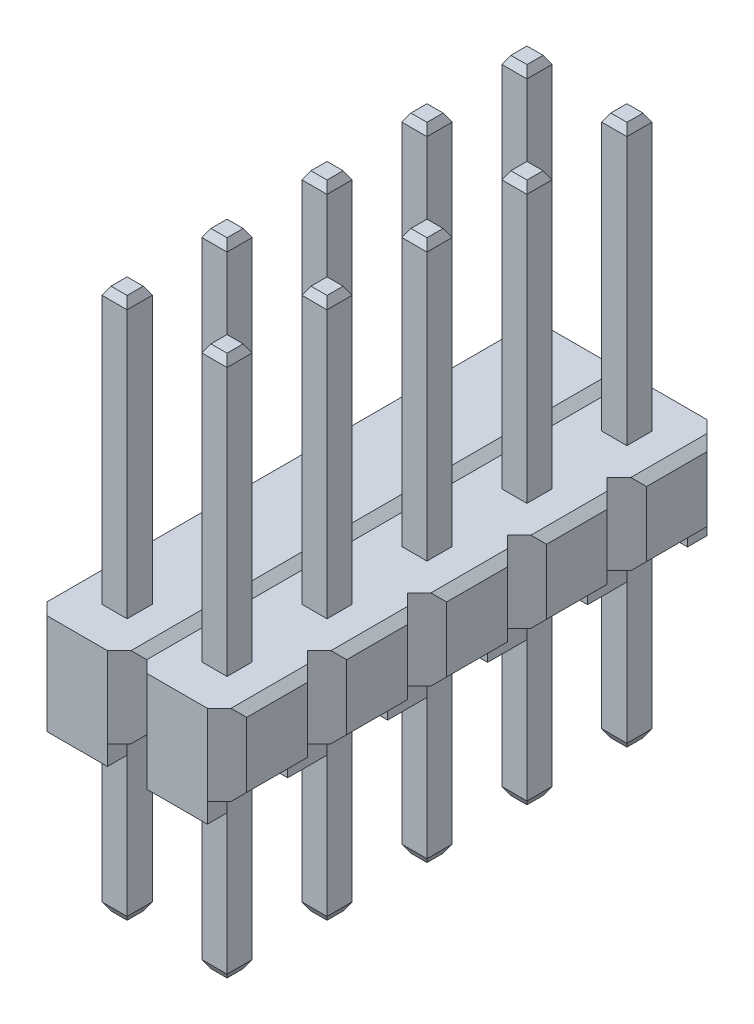
SolidWorks part; units mm, degrees
ref_plane "Front Plane" through (0, 0, 0) normal (0, 0, 1) x (1, 0, 0)
ref_plane "Top Plane" through (0, 0, 0) normal (0, 1, 0) x (1, 0, 0)
ref_plane "Right Plane" through (0, 0, 0) normal (1, 0, 0) x (0, 0, -1)
sketch "Sketch1" plane through (0, 0, 0) normal (0, 1, 0) x (1, 0, 0)
  line L0 (0, 0.77) -> (0.5, 1.27)
  line L1 (0, 4.31) -> (-0.5, 3.81)
  line L2 (2.04, 1.27) -> (2.54, 0.77)
  line L3 (2.54, 0.77) -> (2.54, -0.77)
  line L4 (2.54, -0.77) -> (2.04, -1.27)
  line L5 (-2.54, 0) -> (2.54, 0) construction
  line L6 (0.5, -1.27) -> (0, -0.77)
  line L7 (-2.54, 3.31) -> (-2.04, 3.81)
  line L8 (-55, 0) -> (55, 0) construction
  line L9 (-2.54, -0.77) -> (-2.54, 0.77)
  line L10 (-1.59, -0.32) -> (-0.95, -0.32)
  line L11 (0.95, -0.32) -> (1.59, -0.32)
  line L12 (0.95, -0.32) -> (0.95, 0.32)
  line L13 (0.95, 0.32) -> (1.59, 0.32)
  line L14 (1.59, -0.32) -> (1.59, 0.32)
  line L15 (-2.54, 0.77) -> (-2.04, 1.27)
  line L16 (-0.95, -0.32) -> (-0.95, 0.32)
  line L17 (-1.59, 0.32) -> (-0.95, 0.32)
  line L18 (0, -0.77) -> (-0.5, -1.27)
  line L19 (-2.04, -1.27) -> (-2.54, -0.77)
  line L20 (-0.5, 3.81) -> (0, 3.31)
  line L21 (-1.59, -0.32) -> (-1.59, 0.32)
  line L22 (1.59, 4.76) -> (1.59, 5.4)
  line L23 (-0.5, 1.27) -> (0, 0.77)
  line L24 (2.04, 3.81) -> (2.54, 3.31)
  line L25 (2.54, 1.77) -> (2.04, 1.27)
  line L26 (0, -55) -> (0, 55) construction
  line L27 (0.95, 2.86) -> (1.59, 2.86)
  line L28 (0.95, 2.22) -> (1.59, 2.22)
  line L29 (-2.54, 1.77) -> (-2.54, 3.31)
  line L30 (-1.59, 2.22) -> (-1.59, 2.86)
  line L31 (-0.95, 2.22) -> (-0.95, 2.86)
  line L32 (0, 1.77) -> (-0.5, 1.27)
  line L35 (2.54, 3.31) -> (2.54, 1.77)
  line L36 (0, 3.31) -> (0.5, 3.81)
  line L37 (0.5, 1.27) -> (0, 1.77)
  line L38 (-1.59, 2.22) -> (-0.95, 2.22)
  line L39 (0.95, 2.22) -> (0.95, 2.86)
  line L40 (1.59, 2.22) -> (1.59, 2.86)
  line L41 (-2.04, 1.27) -> (-2.54, 1.77)
  line L42 (-1.59, 2.86) -> (-0.95, 2.86)
  line L43 (0, -4.31) -> (0.5, -3.81)
  line L44 (-2.04, 6.35) -> (-0.5, 6.35)
  line L45 (-0.5, 6.35) -> (0, 5.85)
  line L46 (-1.59, 4.76) -> (-1.59, 5.4)
  line L47 (0.95, 4.76) -> (1.59, 4.76)
  line L48 (2.54, 5.85) -> (2.54, 4.31)
  line L49 (-2.04, 3.81) -> (-2.54, 4.31)
  line L50 (2.04, -3.81) -> (2.54, -4.31)
  line L51 (-1.59, 4.76) -> (-0.95, 4.76)
  line L52 (2.54, -4.31) -> (2.54, -5.85)
  line L53 (0, 5.85) -> (0.5, 6.35)
  line L54 (2.54, 4.31) -> (2.04, 3.81)
  line L55 (2.04, 6.35) -> (2.54, 5.85)
  line L56 (0.95, 5.4) -> (1.59, 5.4)
  line L57 (-2.54, 5.85) -> (-2.04, 6.35)
  line L58 (-2.54, 4.31) -> (-2.54, 5.85)
  line L59 (-1.59, 5.4) -> (-0.95, 5.4)
  line L60 (-0.95, 4.76) -> (-0.95, 5.4)
  line L61 (0.5, 3.81) -> (0, 4.31)
  line L62 (0.5, 6.35) -> (2.04, 6.35)
  line L63 (0.95, 4.76) -> (0.95, 5.4)
  line L64 (2.54, -5.85) -> (2.04, -6.35)
  line L65 (2.04, -6.35) -> (0.5, -6.35)
  line L66 (0.5, -6.35) -> (0, -5.85)
  line L67 (-2.54, -1.77) -> (-2.04, -1.27)
  line L68 (-0.5, -6.35) -> (-2.04, -6.35)
  line L69 (-2.54, -5.85) -> (-2.54, -4.31)
  line L70 (-1.59, -5.4) -> (-0.95, -5.4)
  line L71 (0.95, -5.4) -> (1.59, -5.4)
  line L72 (0.95, -5.4) -> (0.95, -4.76)
  line L73 (0.95, -4.76) -> (1.59, -4.76)
  line L74 (1.59, -5.4) -> (1.59, -4.76)
  line L75 (-2.54, -4.31) -> (-2.04, -3.81)
  line L76 (-0.95, -5.4) -> (-0.95, -4.76)
  line L77 (-1.59, -4.76) -> (-0.95, -4.76)
  line L78 (0, -5.85) -> (-0.5, -6.35)
  line L79 (-2.04, -6.35) -> (-2.54, -5.85)
  line L80 (-0.5, -1.27) -> (0, -1.77)
  line L81 (-1.59, -5.4) -> (-1.59, -4.76)
  line L82 (-0.5, -3.81) -> (0, -4.31)
  line L83 (2.04, -1.27) -> (2.54, -1.77)
  line L84 (2.54, -3.31) -> (2.04, -3.81)
  line L86 (0.95, -2.22) -> (1.59, -2.22)
  line L87 (0.95, -2.86) -> (1.59, -2.86)
  line L88 (-2.54, -3.31) -> (-2.54, -1.77)
  line L89 (-1.59, -2.86) -> (-1.59, -2.22)
  line L90 (-0.95, -2.86) -> (-0.95, -2.22)
  line L91 (0, -3.31) -> (-0.5, -3.81)
  line L92 (2.54, -1.77) -> (2.54, -3.31)
  line L93 (0, -1.77) -> (0.5, -1.27)
  line L94 (0.5, -3.81) -> (0, -3.31)
  line L95 (-1.59, -2.86) -> (-0.95, -2.86)
  line L96 (0.95, -2.86) -> (0.95, -2.22)
  line L97 (1.59, -2.86) -> (1.59, -2.22)
  line L98 (-2.04, -3.81) -> (-2.54, -3.31)
  line L99 (-1.59, -2.22) -> (-0.95, -2.22)
  dimension "D1" = 12.7
  dimension "D2" = 6.35
  dimension "D3" = 5.08
  dimension "D4" = 2.54
  dimension "D5" = 2.54
extrude "Boss-Extrude1" add sketch "Sketch1" against normal blind 2.05
sketch "Sketch2" plane through (0, 0, 0) normal (0, 0, 1) x (1, 0, 0)
  line L0 (-2.54, -0.2) -> (-2.34, 0)
  line L1 (-2.54, -2.05) -> (-2.54, 0) construction
  line L2 (-2.54, 0) -> (-2.04, 0) construction
  line L3 (-2.34, 0) -> (-2.54, 0)
  line L4 (-2.54, 0) -> (-2.54, -0.2)
  line L5 (-0.2, 0) -> (0.2, 0)
  line L6 (-0.5, 0) -> (0, 0) construction
  line L7 (0, 0) -> (0.5, 0) construction
  line L8 (0.2, 0) -> (0, -0.2)
  line L9 (0, -2.05) -> (0, 0) construction
  line L10 (0, -0.2) -> (-0.2, 0)
  line L11 (2.54, 0) -> (2.34, 0)
  line L12 (2.04, 0) -> (2.54, 0) construction
  line L13 (2.34, 0) -> (2.54, -0.2)
  line L14 (2.54, -2.05) -> (2.54, 0) construction
  line L15 (2.54, -0.2) -> (2.54, 0)
  line L16 (-2.54, -1.025) -> (2.54, -1.025) construction
  line L17 (2.54, -1.85) -> (2.54, -2.05)
  line L18 (2.34, -2.05) -> (2.54, -1.85)
  line L19 (2.54, -2.05) -> (2.34, -2.05)
  line L20 (0, -1.85) -> (-0.2, -2.05)
  line L21 (0.2, -2.05) -> (0, -1.85)
  line L22 (-0.2, -2.05) -> (0.2, -2.05)
  line L23 (-2.54, -2.05) -> (-2.54, -1.85)
  line L24 (-2.34, -2.05) -> (-2.54, -2.05)
  line L25 (-2.54, -1.85) -> (-2.34, -2.05)
  dimension "D1" = 0.2
extrude "Cut-Extrude1" cut sketch "Sketch2" against normal mid plane 20
sketch "Sketch3" plane through (0, -2.05, 0) normal (0, -1, 0) x (1, 0, 0)
  line L0 (2.04, -6.35) -> (0.5, -6.35) construction
  line L1 (-2.04, 6.35) -> (-0.5, 6.35)
  line L2 (-2.04, 6.35) -> (-2.04, 5.85)
  line L3 (-2.04, 5.85) -> (-0.5, 5.85)
  line L4 (-0.5, 6.35) -> (-0.5, 5.85)
  line L5 (0.5, 6.35) -> (2.04, 6.35)
  line L6 (0.5, 6.35) -> (0.5, 5.85)
  line L7 (0.5, 5.85) -> (2.04, 5.85)
  line L8 (2.04, 6.35) -> (2.04, 5.85)
  line L9 (-2.04, -0.77) -> (-0.5, -0.77)
  line L10 (-2.04, -0.77) -> (-2.04, -1.77)
  line L11 (-2.04, -1.77) -> (-0.5, -1.77)
  line L12 (-0.5, -0.77) -> (-0.5, -1.77)
  line L13 (0.5, -0.77) -> (2.04, -0.77)
  line L14 (0.5, -0.77) -> (0.5, -1.77)
  line L15 (0.5, -1.77) -> (2.04, -1.77)
  line L16 (2.04, -0.77) -> (2.04, -1.77)
  line L17 (-2.04, -3.31) -> (-0.5, -3.31)
  line L18 (-2.04, -3.31) -> (-2.04, -4.31)
  line L19 (-2.04, -4.31) -> (-0.5, -4.31)
  line L20 (-0.5, -3.31) -> (-0.5, -4.31)
  line L21 (0.5, -3.31) -> (2.04, -3.31)
  line L22 (0.5, -3.31) -> (0.5, -4.31)
  line L23 (0.5, -4.31) -> (2.04, -4.31)
  line L24 (2.04, -3.31) -> (2.04, -4.31)
  line L25 (-2.04, -6.35) -> (-0.5, -6.35)
  line L26 (-2.04, -6.35) -> (-2.04, -5.85)
  line L27 (-2.04, -5.85) -> (-0.5, -5.85)
  line L28 (-0.5, -6.35) -> (-0.5, -5.85)
  line L29 (0.5, -6.35) -> (2.04, -6.35)
  line L30 (0.5, -6.35) -> (0.5, -5.85)
  line L31 (0.5, -5.85) -> (2.04, -5.85)
  line L32 (2.04, -6.35) -> (2.04, -5.85)
  line L34 (-2.04, 4.31) -> (-0.5, 4.31)
  line L35 (-2.04, 4.31) -> (-2.04, 3.31)
  line L36 (-2.04, 3.31) -> (-0.5, 3.31)
  line L37 (-0.5, 4.31) -> (-0.5, 3.31)
  line L38 (-2.04, 1.77) -> (-0.5, 1.77)
  line L39 (-2.04, 1.77) -> (-2.04, 0.77)
  line L40 (-2.04, 0.77) -> (-0.5, 0.77)
  line L41 (-0.5, 1.77) -> (-0.5, 0.77)
  line L42 (0.5, 4.31) -> (2.04, 4.31)
  line L43 (0.5, 4.31) -> (0.5, 3.31)
  line L44 (0.5, 3.31) -> (2.04, 3.31)
  line L45 (2.04, 4.31) -> (2.04, 3.31)
  line L46 (0.5, 1.77) -> (2.04, 1.77)
  line L47 (0.5, 1.77) -> (0.5, 0.77)
  line L48 (0.5, 0.77) -> (2.04, 0.77)
  line L49 (2.04, 1.77) -> (2.04, 0.77)
  dimension "D1" = 0.5
  dimension "D2" = 1
extrude "Boss-Extrude2" add sketch "Sketch3" along normal blind 0.5
sketch "Sketch4" plane through (0, 0, 0) normal (0, 1, 0) x (1, 0, 0)
  line L1 (-1.59, 5.4) -> (-0.95, 5.4)
  line L2 (-1.59, 5.4) -> (-1.59, 4.76)
  line L3 (-1.59, 4.76) -> (-0.95, 4.76)
  line L4 (-0.95, 5.4) -> (-0.95, 4.76)
  line L5 (0.95, 5.4) -> (1.59, 5.4)
  line L6 (0.95, 5.4) -> (0.95, 4.76)
  line L7 (0.95, 4.76) -> (1.59, 4.76)
  line L8 (1.59, 5.4) -> (1.59, 4.76)
  line L9 (-1.59, 2.86) -> (-0.95, 2.86)
  line L10 (-1.59, 2.86) -> (-1.59, 2.22)
  line L11 (-1.59, 2.22) -> (-0.95, 2.22)
  line L12 (-0.95, 2.86) -> (-0.95, 2.22)
  line L13 (0.95, 2.86) -> (1.59, 2.86)
  line L14 (0.95, 2.86) -> (0.95, 2.22)
  line L15 (0.95, 2.22) -> (1.59, 2.22)
  line L16 (1.59, 2.86) -> (1.59, 2.22)
  line L17 (-1.59, 0.32) -> (-0.95, 0.32)
  line L18 (-1.59, 0.32) -> (-1.59, -0.32)
  line L19 (-1.59, -0.32) -> (-0.95, -0.32)
  line L20 (-0.95, 0.32) -> (-0.95, -0.32)
  line L21 (0.95, 0.32) -> (1.59, 0.32)
  line L22 (0.95, 0.32) -> (0.95, -0.32)
  line L23 (0.95, -0.32) -> (1.59, -0.32)
  line L24 (1.59, 0.32) -> (1.59, -0.32)
  line L25 (-1.59, -2.22) -> (-0.95, -2.22)
  line L26 (-1.59, -2.22) -> (-1.59, -2.86)
  line L27 (-1.59, -2.86) -> (-0.95, -2.86)
  line L28 (-0.95, -2.22) -> (-0.95, -2.86)
  line L29 (0.95, -2.22) -> (1.59, -2.22)
  line L30 (0.95, -2.22) -> (0.95, -2.86)
  line L31 (0.95, -2.86) -> (1.59, -2.86)
  line L32 (1.59, -2.22) -> (1.59, -2.86)
  line L33 (-1.59, -4.76) -> (-0.95, -4.76)
  line L34 (-1.59, -4.76) -> (-1.59, -5.4)
  line L35 (-1.59, -5.4) -> (-0.95, -5.4)
  line L36 (-0.95, -4.76) -> (-0.95, -5.4)
  line L37 (0.95, -4.76) -> (1.59, -4.76)
  line L38 (0.95, -4.76) -> (0.95, -5.4)
  line L39 (0.95, -5.4) -> (1.59, -5.4)
  line L40 (1.59, -4.76) -> (1.59, -5.4)
extrude "Boss-Extrude3" add sketch "Sketch4" along normal blind 7 and the other way offset from surface (6.75 mm away) 4.7 other way up to face at (-1.27, -2.05, -2.54)
chamfer "Chamfer1" distance 0.2 angle 30 80 edges at (-1.27, -6.75, 0.32) (-0.95, -6.75, 0) (-1.27, -6.75, -0.32) (-1.59, -6.75, 0) (-1.27, -6.75, -2.22) (-0.95, -6.75, -2.54) (-1.27, -6.75, -2.86) (-1.59, -6.75, -2.54) (-1.27, -6.75, -4.76) (-0.95, -6.75, -5.08) (-1.27, -6.75, -5.4) (-1.59, -6.75, -5.08) (1.27, -6.75, 0.32) (1.59, -6.75, 0) (1.27, -6.75, -0.32) (0.95, -6.75, 0) (1.27, -6.75, -2.22) (1.59, -6.75, -2.54) (1.27, -6.75, -2.86) (0.95, -6.75, -2.54) (1.27, -6.75, -4.76) (1.59, -6.75, -5.08) (1.27, -6.75, -5.4) (0.95, -6.75, -5.08) (-1.27, 7, -0.32) (-0.95, 7, 0) (-1.27, 7, 0.32) (-1.59, 7, 0) (-1.27, 7, -2.86) (-0.95, 7, -2.54) (-1.27, 7, -2.22) (-1.59, 7, -2.54) (-1.27, 7, -5.4) (-0.95, 7, -5.08) (-1.27, 7, -4.76) (-1.59, 7, -5.08) (1.27, 7, -0.32) (1.59, 7, 0) (1.27, 7, 0.32) (0.95, 7, 0) (1.27, 7, -2.86) (1.59, 7, -2.54) (1.27, 7, -2.22) (0.95, 7, -2.54) (1.27, 7, -5.4) (1.59, 7, -5.08) (1.27, 7, -4.76) (0.95, 7, -5.08) (1.27, -6.75, 2.86) (1.59, -6.75, 2.54) (1.27, -6.75, 2.22) (0.95, -6.75, 2.54) (-1.27, -6.75, 2.86) (-0.95, -6.75, 2.54) (-1.27, -6.75, 2.22) (-1.59, -6.75, 2.54) (-1.27, -6.75, 5.4) (-0.95, -6.75, 5.08) (-1.27, -6.75, 4.76) (-1.59, -6.75, 5.08) (1.27, -6.75, 5.4) (1.59, -6.75, 5.08) (1.27, -6.75, 4.76) (0.95, -6.75, 5.08) (1.27, 7, 4.76) (1.59, 7, 5.08) (1.27, 7, 5.4) (0.95, 7, 5.08) (-1.27, 7, 4.76) (-0.95, 7, 5.08) (-1.27, 7, 5.4) (-1.59, 7, 5.08) (1.27, 7, 2.22) (1.59, 7, 2.54) (1.27, 7, 2.86) (0.95, 7, 2.54) (-1.27, 7, 2.22) (-0.95, 7, 2.54) (-1.27, 7, 2.86) (-1.59, 7, 2.54)
sketch "Sketch5" plane through (0, -6.75, 0) normal (0, -1, 0) x (1, 0, 0)
  line L0 (-1.4745, -4.8755) -> (-1.0655, -5.2845) construction
  line L1 (-1.0655, -5.2845) -> (-1.0655, -4.8755) construction
  line L2 (-1.0655, -4.8755) -> (-1.4745, -5.2845) construction
  line L3 (-1.4745, 5.2845) -> (-1.0655, 4.8755) construction
  line L4 (-1.0655, 4.8755) -> (-1.0655, 5.2845) construction
  line L5 (-1.0655, 5.2845) -> (-1.4745, 4.8755) construction
  line L6 (-1.4745, 4.8755) -> (-1.0655, 4.8755) construction
  circle A0 centre (-1.27, -5.08) radius 0.125
  circle A1 centre (-1.27, 5.08) radius 0.125
  dimension "D1" = 0.25
extrude "Cut-Extrude2" cut sketch "Sketch5" against normal blind 1
scale "Scale1" scale about centroid uniform scaling yes scale factor 0.5
